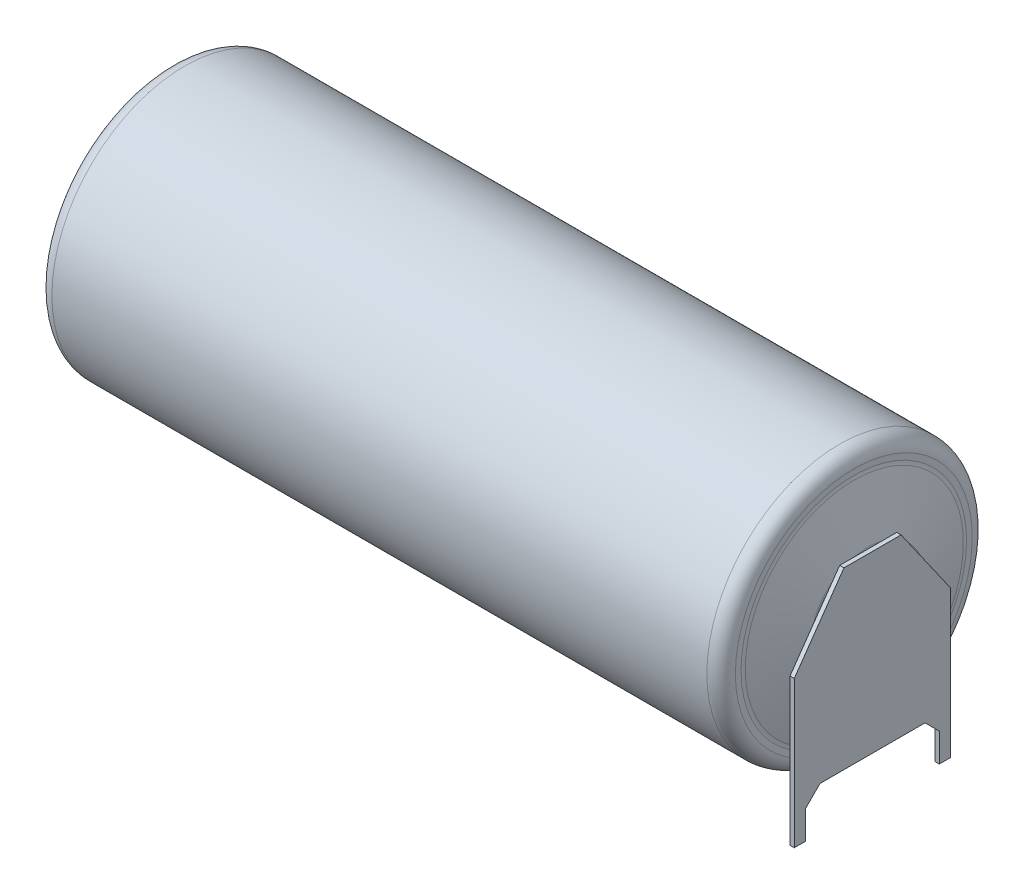
SolidWorks part; units mm, degrees
ref_plane "Front Plane" through (0, 0, 0) normal (0, 0, 1) x (1, 0, 0)
ref_plane "Top Plane" through (0, 0, 0) normal (0, 1, 0) x (1, 0, 0)
ref_plane "Right Plane" through (0, 0, 0) normal (1, 0, 0) x (0, 0, -1)
sketch "Sketch1" plane through (0, 0, 0) normal (0, 0, 1) x (1, 0, 0)
  line L0 (-25.25, 0) -> (24.45, 0)
  line L1 (24.2403, 8.3) -> (24.2403, 7.9)
  line L2 (-22.65, 9.3) -> (23.2403, 9.3)
  line L3 (25.25, 0.5) -> (-25.25, 0.5) construction
  line L4 (0, 0) -> (0, 0.5) construction
  line L5 (-23.65, 8.3) -> (-23.65, 7.4)
  line L6 (-23.55, 7.3) -> (-23.25, 7.3)
  line L7 (24.2743, 7.6412) -> (25.2364, 4.0509)
  line L8 (25.25, 3.9473) -> (25.25, 0.9)
  line L9 (25.15, 0.8) -> (24.55, 0.8)
  line L10 (24.45, 0.7) -> (24.45, 0)
  line L11 (-25.25, 0) -> (-25.25, 2.1)
  line L12 (-23.15, 7.2) -> (-23.15, 4.35)
  line L13 (-24.85, 2.5) -> (-23.85, 2.5)
  line L14 (-23.45, 2.9) -> (-23.45, 4.15)
  line L15 (-23.35, 4.25) -> (-23.25, 4.25)
  arc A0 (-23.65, 8.3) -> (-22.65, 9.3) centre (-22.65, 8.3) cw
  arc A1 (25.2364, 4.0509) -> (25.25, 3.9473) centre (24.85, 3.9473) cw
  arc A2 (-23.45, 2.9) -> (-23.85, 2.5) centre (-23.85, 2.9) cw
  arc A3 (-25.25, 2.1) -> (-24.85, 2.5) centre (-24.85, 2.1) cw
  arc A4 (23.2403, 9.3) -> (24.2403, 8.3) centre (23.2403, 8.3) cw
  arc A5 (24.2743, 7.6412) -> (24.2403, 7.9) centre (25.2403, 7.9) cw
  arc A6 (24.45, 0.7) -> (24.55, 0.8) centre (24.55, 0.7) cw
  arc A7 (25.25, 0.9) -> (25.15, 0.8) centre (25.15, 0.9) cw
  arc A8 (-23.65, 7.4) -> (-23.55, 7.3) centre (-23.55, 7.4) ccw
  arc A9 (-23.25, 7.3) -> (-23.15, 7.2) centre (-23.25, 7.2) cw
  arc A10 (-23.25, 4.25) -> (-23.15, 4.35) centre (-23.25, 4.35) ccw
  arc A11 (-23.35, 4.25) -> (-23.45, 4.15) centre (-23.35, 4.15) ccw
  point P5 (24.2403, 7.7683)
  point P20 (25.25, 4)
  point P26 (-23.65, 9.3)
  point P30 (24.2403, 7.7683)
  point P37 (-23.65, 7.3)
  dimension "D8" = 9.3
  dimension "D4" = 1
  dimension "D5" = 1
  dimension "D16" = 0.4
  dimension "D17" = 0.1
  dimension "D1" = 0.8
  dimension "D2" = 0.8
  dimension "D3" = 15
  dimension "D6" = 4
  dimension "D7" = 2
  dimension "D9" = 0.5
  dimension "D10" = 2.5
  dimension "D11" = 4.25
  dimension "D12" = 1.6
  dimension "D13" = 0.3
  dimension "D14" = 50.5
  dimension "D15" = 0.4
  dimension "D18" = 0.5
revolve "Revolve1" add sketch "Sketch1" angle 360 about L0
sketch "Sketch2" plane through (25.25, 0, 0) normal (1, 0, 0) x (0, 0, -1)
  line L0 (0, 0) -> (0, 3.9473) construction
  line L1 (-2, 3.9473) -> (2, 3.9473)
  line L5 (0, -9.3) -> (0, 0) construction
  line L6 (-3.68, -8.3) -> (3.68, -8.3)
  line L7 (3.68, -8.3) -> (4.68, -9.3)
  line L8 (4.68, -9.3) -> (4.68, -11.3)
  line L9 (4.68, -11.3) -> (5.48, -11.3)
  line L10 (5.48, -11.3) -> (5.48, -1.0226)
  line L11 (5.48, -1.0226) -> (2, 3.9473)
  line L12 (-5.48, -1.0226) -> (-2, 3.9473)
  line L13 (-5.48, -1.0226) -> (-5.48, -11.3)
  line L14 (-5.48, -11.3) -> (-4.68, -11.3)
  line L15 (-4.68, -11.3) -> (-4.68, -9.3)
  line L16 (-4.68, -9.3) -> (-3.68, -8.3)
  line L18 (5.08, -11.3) -> (5.08, -14.6309) construction
  line L19 (-5.08, -11.3) -> (-5.08, -14.0379) construction
  line L20 (0, -9.3) -> (0, -8.3) construction
  circle A0 centre (0, 0) radius 9.3 construction
  circle A1 centre (0, 0) radius 3.9473 construction
  point P7 (0, -9.3)
  dimension "D1" = 2
  dimension "D2" = 1
  dimension "D3" = 10.16
  dimension "D4" = 0.8
  dimension "D5" = 45
  dimension "D6" = 1
  dimension "D8" = 35
  dimension "D9" = 4
extrude "Boss-Extrude1" add sketch "Sketch2" along normal blind 0.3
sketch "Sketch3" plane through (-25.25, 0, 0) normal (-1, 0, 0) x (0, 0, 1)
  line L0 (0, 0) -> (0, 3) construction
  line L1 (-1.75, 3) -> (1.75, 3)
  line L2 (-1.75, 3) -> (-1.75, -7.8)
  line L3 (0, -11.3) -> (0, 0) construction
  line L4 (1.75, 3) -> (1.75, -7.8)
  line L5 (-1.75, -7.8) -> (-0.4, -8.8)
  line L6 (-0.4, -8.8) -> (-0.4, -11.3)
  line L7 (-0.4, -11.3) -> (0.4, -11.3)
  line L8 (0.4, -11.3) -> (0.4, -8.8)
  line L9 (0.4, -8.8) -> (1.75, -7.8)
  line L10 (5.48, -11.3) -> (4.68, -11.3) construction
  dimension "D1" = 3
  dimension "D2" = 3.5
  dimension "D3" = 0.8
  dimension "D4" = 2.5
  dimension "D5" = 1
extrude "Boss-Extrude2" add sketch "Sketch3" along normal blind 0.3
